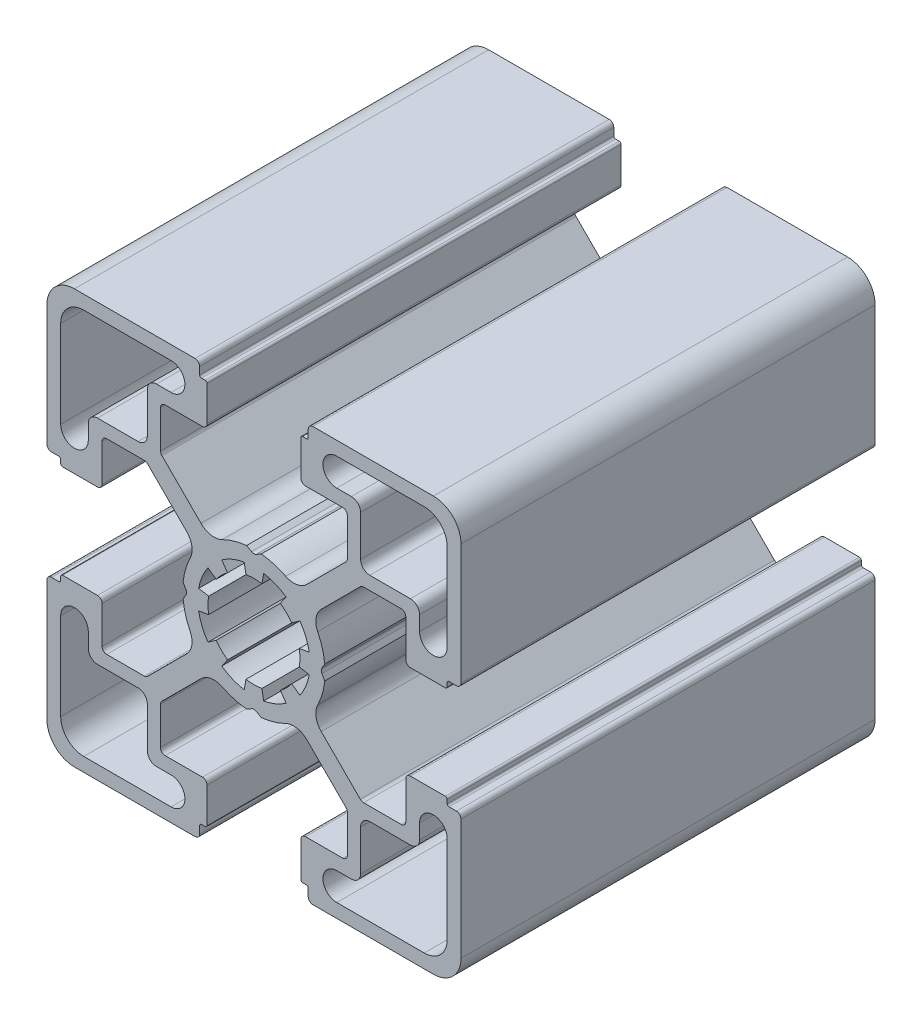
SolidWorks part; units mm, degrees
material "АД31Т ГОСТ 4784-97"
ref_plane "Спереди" through (0, 0, 0) normal (0, 0, 1) x (1, 0, 0)
ref_plane "Сверху" through (0, 0, 0) normal (0, 1, 0) x (1, 0, 0)
ref_plane "Справа" through (0, 0, 0) normal (1, 0, 0) x (0, 0, -1)
sketch "Эскиз1" plane through (0, 0, 0) normal (0, 0, 1) x (1, 0, 0)
  line L1 (11.59, -14.6758) -> (11.59, -12.59)
  line L2 (18.5, 21) -> (9, 21)
  line L3 (-11.59, 14.6758) -> (-11.59, 12.59)
  line L4 (18, 10.59) -> (18, 9)
  line L5 (14.6758, 11.59) -> (17, 11.59)
  line L6 (14.6758, 11.59) -> (12.59, 11.59)
  line L7 (21, 18.5) -> (21, 9)
  line L8 (-7.3858, -0.25) -> (-7.7005, -0.7951)
  line L9 (-2.8679, 4.0958) -> (-3.4988, 4.9968)
  line L10 (-16.5, 5.6) -> (-16.5, 9.65)
  line L11 (-16, 10.15) -> (-11.9127, 10.15)
  line L12 (-22, 5.9) -> (-21.2, 5.9)
  line L13 (-20.8, 5.1) -> (-17, 5.1)
  line L14 (-21, 5.7) -> (-21, 5.3)
  line L15 (-22, 5.9) -> (-21.2, 5.9)
  line L16 (11.59, 14.6758) -> (11.59, 17)
  line L17 (-7.8879, 6.3322) -> (-7.308, 5.7523)
  line L18 (-21, 5.7) -> (-21, 5.3)
  line L19 (-7.8879, 6.3322) -> (-11.5592, 10.0036)
  line L20 (-0.25, 7.3858) -> (-0.7951, 7.7005)
  line L21 (-22.5, 6.4) -> (-22.5, 19.5)
  line L22 (10.59, 18) -> (9, 18)
  line L23 (-0.25, 7.3858) -> (-0.7951, 7.7005)
  line L24 (5.6, 16.5) -> (9.65, 16.5)
  line L25 (-6.4, 22.5) -> (-19.5, 22.5)
  line L26 (10.15, 16) -> (10.15, 11.9127)
  line L27 (-6.3322, 7.8879) -> (-10.0036, 11.5592)
  line L28 (-5.7, 21) -> (-5.3, 21)
  line L29 (-7.3858, 0.25) -> (-7.7005, 0.7951)
  line L30 (-6.3322, 7.8879) -> (-5.7523, 7.308)
  line L31 (-5.9, 22) -> (-5.9, 21.2)
  line L32 (-5.7, 21) -> (-5.3, 21)
  line L33 (-5.1, 20.8) -> (-5.1, 17)
  line L34 (-5.9, 22) -> (-5.9, 21.2)
  line L35 (-10.15, 16) -> (-10.15, 11.9127)
  line L36 (-5.6, 16.5) -> (-9.65, 16.5)
  line L37 (0.25, 7.3858) -> (0.7951, 7.7005)
  line L38 (-10.59, 18) -> (-9, 18)
  line L39 (-11.59, 14.6758) -> (-11.59, 17)
  line L40 (-21, 18.5) -> (-21, 9)
  line L41 (5.9, 22) -> (5.9, 21.2)
  line L42 (-14.6758, 11.59) -> (-12.59, 11.59)
  line L43 (-14.6758, 11.59) -> (-17, 11.59)
  line L44 (-18, 10.59) -> (-18, 9)
  line L45 (5.1, 20.8) -> (5.1, 17)
  line L46 (-18.5, 21) -> (-9, 21)
  line L47 (5.7, 21) -> (5.3, 21)
  line L48 (5.9, 22) -> (5.9, 21.2)
  line L49 (6.3322, 7.8879) -> (5.7523, 7.308)
  line L50 (7.3858, 0.25) -> (7.7005, 0.7951)
  line L51 (5.7, 21) -> (5.3, 21)
  line L52 (6.3322, 7.8879) -> (10.0036, 11.5592)
  line L53 (6.4, 22.5) -> (19.5, 22.5)
  line L54 (22.5, 6.4) -> (22.5, 19.5)
  line L55 (0.25, 7.3858) -> (0.7951, 7.7005)
  line L56 (7.8879, 6.3322) -> (11.5592, 10.0036)
  line L57 (21, 5.7) -> (21, 5.3)
  line L58 (7.8879, 6.3322) -> (7.308, 5.7523)
  line L59 (22, 5.9) -> (21.2, 5.9)
  line L60 (21, 5.7) -> (21, 5.3)
  line L61 (20.8, 5.1) -> (17, 5.1)
  line L62 (22, 5.9) -> (21.2, 5.9)
  line L63 (16, 10.15) -> (11.9127, 10.15)
  line L64 (16.5, 5.6) -> (16.5, 9.65)
  line L65 (7.3858, -0.25) -> (7.7005, -0.7951)
  line L66 (11.59, 14.6758) -> (11.59, 12.59)
  line L67 (7.3858, 0.25) -> (7.7005, 0.7951)
  line L68 (16.5, -5.6) -> (16.5, -9.65)
  line L69 (16, -10.15) -> (11.9127, -10.15)
  line L70 (22, -5.9) -> (21.2, -5.9)
  line L71 (20.8, -5.1) -> (17, -5.1)
  line L72 (21, -5.7) -> (21, -5.3)
  line L73 (22, -5.9) -> (21.2, -5.9)
  line L74 (7.8879, -6.3322) -> (7.308, -5.7523)
  line L75 (21, -5.7) -> (21, -5.3)
  line L76 (7.8879, -6.3322) -> (11.5592, -10.0036)
  line L77 (0.25, -7.3858) -> (0.7951, -7.7005)
  line L78 (22.5, -6.4) -> (22.5, -19.5)
  line L79 (6.4, -22.5) -> (19.5, -22.5)
  line L80 (6.3322, -7.8879) -> (10.0036, -11.5592)
  line L81 (5.7, -21) -> (5.3, -21)
  line L82 (7.3858, -0.25) -> (7.7005, -0.7951)
  line L83 (6.3322, -7.8879) -> (5.7523, -7.308)
  line L84 (5.9, -22) -> (5.9, -21.2)
  line L85 (5.7, -21) -> (5.3, -21)
  line L86 (-18.5, -21) -> (-9, -21)
  line L87 (5.1, -20.8) -> (5.1, -17)
  line L88 (-18, -10.59) -> (-18, -9)
  line L89 (-14.6758, -11.59) -> (-17, -11.59)
  line L90 (-14.6758, -11.59) -> (-12.59, -11.59)
  line L91 (5.9, -22) -> (5.9, -21.2)
  line L92 (-21, -18.5) -> (-21, -9)
  line L93 (-11.59, -14.6758) -> (-11.59, -17)
  line L94 (-10.59, -18) -> (-9, -18)
  line L95 (0.25, -7.3858) -> (0.7951, -7.7005)
  line L96 (-5.6, -16.5) -> (-9.65, -16.5)
  line L97 (-10.15, -16) -> (-10.15, -11.9127)
  line L98 (-5.9, -22) -> (-5.9, -21.2)
  line L99 (-5.1, -20.8) -> (-5.1, -17)
  line L100 (-5.7, -21) -> (-5.3, -21)
  line L101 (-5.9, -22) -> (-5.9, -21.2)
  line L102 (-6.3322, -7.8879) -> (-5.7523, -7.308)
  line L103 (-7.3858, -0.25) -> (-7.7005, -0.7951)
  line L104 (-5.7, -21) -> (-5.3, -21)
  line L105 (-6.3322, -7.8879) -> (-10.0036, -11.5592)
  line L106 (10.15, -16) -> (10.15, -11.9127)
  line L107 (-6.4, -22.5) -> (-19.5, -22.5)
  line L108 (5.6, -16.5) -> (9.65, -16.5)
  line L109 (-0.25, -7.3858) -> (-0.7951, -7.7005)
  line L110 (10.59, -18) -> (9, -18)
  line L111 (-22.5, -6.4) -> (-22.5, -19.5)
  line L112 (-0.25, -7.3858) -> (-0.7951, -7.7005)
  line L113 (-7.8879, -6.3322) -> (-11.5592, -10.0036)
  line L114 (-21, -5.7) -> (-21, -5.3)
  line L115 (-7.8879, -6.3322) -> (-7.308, -5.7523)
  line L116 (11.59, -14.6758) -> (11.59, -17)
  line L117 (-22, -5.9) -> (-21.2, -5.9)
  line L118 (-21, -5.7) -> (-21, -5.3)
  line L119 (-20.8, -5.1) -> (-17, -5.1)
  line L120 (-22, -5.9) -> (-21.2, -5.9)
  line L121 (-16, -10.15) -> (-11.9127, -10.15)
  line L122 (-16.5, -5.6) -> (-16.5, -9.65)
  line L123 (-7.3858, 0.25) -> (-7.7005, 0.7951)
  line L124 (21, -18.5) -> (21, -9)
  line L125 (14.6758, -11.59) -> (12.59, -11.59)
  line L126 (14.6758, -11.59) -> (17, -11.59)
  line L127 (18, -10.59) -> (18, -9)
  line L128 (-11.59, -14.6758) -> (-11.59, -12.59)
  line L129 (18.5, -21) -> (9, -21)
  line L130 (-4.0958, 2.8679) -> (-4.9968, 3.4988)
  line L131 (-0.8682, 4.924) -> (-1.0593, 6.0073)
  line L132 (0.8682, 4.924) -> (1.0593, 6.0073)
  line L134 (-4.924, -0.8682) -> (-6.0073, -1.0593)
  line L135 (-4.924, 0.8682) -> (-6.0073, 1.0593)
  line L136 (0.8682, -4.924) -> (1.0593, -6.0073)
  line L137 (-0.8682, -4.924) -> (-1.0593, -6.0073)
  line L138 (-2.8679, -4.0958) -> (-3.4988, -4.9968)
  line L139 (-4.0958, -2.8679) -> (-4.9968, -3.4988)
  line L140 (-4.924, -0.8682) -> (-6.0073, -1.0593)
  line L141 (-4.924, 0.8682) -> (-6.0073, 1.0593)
  line L142 (2.8679, 4.0958) -> (3.4988, 4.9968)
  line L143 (4.0958, 2.8679) -> (4.9968, 3.4988)
  line L144 (4.924, 0.8682) -> (6.0073, 1.0593)
  line L145 (4.924, -0.8682) -> (6.0073, -1.0593)
  line L146 (4.0958, -2.8679) -> (4.9968, -3.4988)
  line L147 (2.8679, -4.0958) -> (3.4988, -4.9968)
  arc A0 (-2.8679, 4.0958) -> (-4.0958, 2.8679) centre (0, 0) ccw
  arc A1 (-4.9968, 3.4988) -> (-6.0073, 1.0593) centre (0, 0) ccw
  arc A2 (-19.5, 22.5) -> (-22.5, 19.5) centre (-19.5, 19.5) ccw
  arc A3 (-11.5592, 10.0036) -> (-11.9127, 10.15) centre (-11.9127, 9.65) ccw
  arc A4 (-16, 10.15) -> (-16.5, 9.65) centre (-16, 9.65) ccw
  arc A5 (-17, 5.1) -> (-16.5, 5.6) centre (-17, 5.6) ccw
  arc A6 (-22.5, 6.4) -> (-22, 5.9) centre (-22, 6.4) ccw
  arc A7 (-20.8, 5.1) -> (-21, 5.3) centre (-20.8, 5.3) cw
  arc A8 (-21.2, 5.9) -> (-21, 5.7) centre (-21.2, 5.7) cw
  arc A9 (-6.9314, 3.4475) -> (-7.7005, 0.7951) centre (0, 0) ccw
  arc A10 (10.59, 18) -> (11.59, 17) centre (10.59, 17) cw
  arc A11 (9, 21) -> (9, 18) centre (9, 19.5) ccw
  arc A12 (17, 11.59) -> (18, 10.59) centre (17, 10.59) cw
  arc A13 (12.59, 11.59) -> (11.59, 12.59) centre (12.59, 12.59) cw
  arc A14 (21, 9) -> (18, 9) centre (19.5, 9) cw
  arc A15 (21, 18.5) -> (18.5, 21) centre (18.5, 18.5) ccw
  arc A16 (-7.308, 5.7523) -> (-6.9314, 3.4475) centre (-8.7222, 4.3381) cw
  arc A17 (-5.9, 21.2) -> (-5.7, 21) centre (-5.7, 21.2) ccw
  arc A18 (-7.3858, -0.25) -> (-7.3858, 0.25) centre (-7.8188, 0) ccw
  arc A19 (-22.5, 6.4) -> (-22, 5.9) centre (-22, 6.4) ccw
  arc A20 (-21.2, 5.9) -> (-21, 5.7) centre (-21.2, 5.7) cw
  arc A21 (-6.4, 22.5) -> (-5.9, 22) centre (-6.4, 22) cw
  arc A22 (0.25, 7.3858) -> (-0.25, 7.3858) centre (0, 7.8188) cw
  arc A23 (-5.7523, 7.308) -> (-3.4475, 6.9314) centre (-4.3381, 8.7222) ccw
  arc A24 (-3.4475, 6.9314) -> (-0.7951, 7.7005) centre (0, 0) cw
  arc A25 (-5.9, 21.2) -> (-5.7, 21) centre (-5.7, 21.2) ccw
  arc A26 (-5.1, 20.8) -> (-5.3, 21) centre (-5.3, 20.8) ccw
  arc A27 (-6.4, 22.5) -> (-5.9, 22) centre (-6.4, 22) cw
  arc A28 (-5.1, 17) -> (-5.6, 16.5) centre (-5.6, 17) cw
  arc A29 (-10.15, 16) -> (-9.65, 16.5) centre (-9.65, 16) cw
  arc A30 (-10.0036, 11.5592) -> (-10.15, 11.9127) centre (-9.65, 11.9127) cw
  arc A31 (-21, 18.5) -> (-18.5, 21) centre (-18.5, 18.5) cw
  arc A32 (-21, 9) -> (-18, 9) centre (-19.5, 9) ccw
  arc A33 (-12.59, 11.59) -> (-11.59, 12.59) centre (-12.59, 12.59) ccw
  arc A34 (-17, 11.59) -> (-18, 10.59) centre (-17, 10.59) ccw
  arc A35 (-9, 21) -> (-9, 18) centre (-9, 19.5) cw
  arc A36 (-10.59, 18) -> (-11.59, 17) centre (-10.59, 17) ccw
  arc A37 (10.0036, 11.5592) -> (10.15, 11.9127) centre (9.65, 11.9127) ccw
  arc A38 (10.15, 16) -> (9.65, 16.5) centre (9.65, 16) ccw
  arc A39 (5.1, 17) -> (5.6, 16.5) centre (5.6, 17) ccw
  arc A40 (6.4, 22.5) -> (5.9, 22) centre (6.4, 22) ccw
  arc A41 (5.1, 20.8) -> (5.3, 21) centre (5.3, 20.8) cw
  arc A42 (5.9, 21.2) -> (5.7, 21) centre (5.7, 21.2) cw
  arc A43 (3.4475, 6.9314) -> (0.7951, 7.7005) centre (0, 0) ccw
  arc A44 (5.7523, 7.308) -> (3.4475, 6.9314) centre (4.3381, 8.7222) cw
  arc A45 (6.4, 22.5) -> (5.9, 22) centre (6.4, 22) ccw
  arc A46 (21.2, 5.9) -> (21, 5.7) centre (21.2, 5.7) ccw
  arc A47 (22.5, 6.4) -> (22, 5.9) centre (22, 6.4) cw
  arc A48 (7.3858, -0.25) -> (7.3858, 0.25) centre (7.8188, 0) cw
  arc A49 (5.9, 21.2) -> (5.7, 21) centre (5.7, 21.2) cw
  arc A50 (7.308, 5.7523) -> (6.9314, 3.4475) centre (8.7222, 4.3381) ccw
  arc A51 (6.9314, 3.4475) -> (7.7005, 0.7951) centre (0, 0) cw
  arc A52 (21.2, 5.9) -> (21, 5.7) centre (21.2, 5.7) ccw
  arc A53 (20.8, 5.1) -> (21, 5.3) centre (20.8, 5.3) ccw
  arc A54 (22.5, 6.4) -> (22, 5.9) centre (22, 6.4) cw
  arc A55 (17, 5.1) -> (16.5, 5.6) centre (17, 5.6) cw
  arc A56 (16, 10.15) -> (16.5, 9.65) centre (16, 9.65) cw
  arc A57 (11.5592, 10.0036) -> (11.9127, 10.15) centre (11.9127, 9.65) cw
  arc A58 (19.5, 22.5) -> (22.5, 19.5) centre (19.5, 19.5) cw
  arc A59 (19.5, -22.5) -> (22.5, -19.5) centre (19.5, -19.5) ccw
  arc A60 (11.5592, -10.0036) -> (11.9127, -10.15) centre (11.9127, -9.65) ccw
  arc A61 (16, -10.15) -> (16.5, -9.65) centre (16, -9.65) ccw
  arc A62 (17, -5.1) -> (16.5, -5.6) centre (17, -5.6) ccw
  arc A63 (22.5, -6.4) -> (22, -5.9) centre (22, -6.4) ccw
  arc A64 (20.8, -5.1) -> (21, -5.3) centre (20.8, -5.3) cw
  arc A65 (21.2, -5.9) -> (21, -5.7) centre (21.2, -5.7) cw
  arc A66 (6.9314, -3.4475) -> (7.7005, -0.7951) centre (0, 0) ccw
  arc A67 (7.308, -5.7523) -> (6.9314, -3.4475) centre (8.7222, -4.3381) cw
  arc A68 (5.9, -21.2) -> (5.7, -21) centre (5.7, -21.2) ccw
  arc A69 (22.5, -6.4) -> (22, -5.9) centre (22, -6.4) ccw
  arc A70 (21.2, -5.9) -> (21, -5.7) centre (21.2, -5.7) cw
  arc A71 (6.4, -22.5) -> (5.9, -22) centre (6.4, -22) cw
  arc A72 (5.7523, -7.308) -> (3.4475, -6.9314) centre (4.3381, -8.7222) ccw
  arc A73 (3.4475, -6.9314) -> (0.7951, -7.7005) centre (0, 0) cw
  arc A74 (5.9, -21.2) -> (5.7, -21) centre (5.7, -21.2) ccw
  arc A75 (5.1, -20.8) -> (5.3, -21) centre (5.3, -20.8) ccw
  arc A76 (6.4, -22.5) -> (5.9, -22) centre (6.4, -22) cw
  arc A77 (5.1, -17) -> (5.6, -16.5) centre (5.6, -17) cw
  arc A78 (10.15, -16) -> (9.65, -16.5) centre (9.65, -16) cw
  arc A79 (10.0036, -11.5592) -> (10.15, -11.9127) centre (9.65, -11.9127) cw
  arc A80 (-10.59, -18) -> (-11.59, -17) centre (-10.59, -17) cw
  arc A81 (-9, -21) -> (-9, -18) centre (-9, -19.5) ccw
  arc A82 (-17, -11.59) -> (-18, -10.59) centre (-17, -10.59) cw
  arc A83 (-12.59, -11.59) -> (-11.59, -12.59) centre (-12.59, -12.59) cw
  arc A84 (-21, -9) -> (-18, -9) centre (-19.5, -9) cw
  arc A85 (-21, -18.5) -> (-18.5, -21) centre (-18.5, -18.5) ccw
  arc A86 (-10.0036, -11.5592) -> (-10.15, -11.9127) centre (-9.65, -11.9127) ccw
  arc A87 (-10.15, -16) -> (-9.65, -16.5) centre (-9.65, -16) ccw
  arc A88 (-5.1, -17) -> (-5.6, -16.5) centre (-5.6, -17) ccw
  arc A89 (-6.4, -22.5) -> (-5.9, -22) centre (-6.4, -22) ccw
  arc A90 (-5.1, -20.8) -> (-5.3, -21) centre (-5.3, -20.8) cw
  arc A91 (-5.9, -21.2) -> (-5.7, -21) centre (-5.7, -21.2) cw
  arc A92 (-3.4475, -6.9314) -> (-0.7951, -7.7005) centre (0, 0) ccw
  arc A93 (-5.7523, -7.308) -> (-3.4475, -6.9314) centre (-4.3381, -8.7222) cw
  arc A94 (0.25, -7.3858) -> (-0.25, -7.3858) centre (0, -7.8188) ccw
  arc A95 (-6.4, -22.5) -> (-5.9, -22) centre (-6.4, -22) ccw
  arc A96 (-21.2, -5.9) -> (-21, -5.7) centre (-21.2, -5.7) ccw
  arc A97 (-22.5, -6.4) -> (-22, -5.9) centre (-22, -6.4) cw
  arc A98 (-5.9, -21.2) -> (-5.7, -21) centre (-5.7, -21.2) cw
  arc A99 (-7.308, -5.7523) -> (-6.9314, -3.4475) centre (-8.7222, -4.3381) ccw
  arc A100 (21, -18.5) -> (18.5, -21) centre (18.5, -18.5) cw
  arc A101 (21, -9) -> (18, -9) centre (19.5, -9) ccw
  arc A102 (12.59, -11.59) -> (11.59, -12.59) centre (12.59, -12.59) ccw
  arc A103 (17, -11.59) -> (18, -10.59) centre (17, -10.59) ccw
  arc A104 (9, -21) -> (9, -18) centre (9, -19.5) cw
  arc A105 (10.59, -18) -> (11.59, -17) centre (10.59, -17) ccw
  arc A106 (-6.9314, -3.4475) -> (-7.7005, -0.7951) centre (0, 0) cw
  arc A107 (-21.2, -5.9) -> (-21, -5.7) centre (-21.2, -5.7) ccw
  arc A108 (-20.8, -5.1) -> (-21, -5.3) centre (-20.8, -5.3) ccw
  arc A109 (-22.5, -6.4) -> (-22, -5.9) centre (-22, -6.4) cw
  arc A110 (-17, -5.1) -> (-16.5, -5.6) centre (-17, -5.6) cw
  arc A111 (-16, -10.15) -> (-16.5, -9.65) centre (-16, -9.65) cw
  arc A112 (-11.5592, -10.0036) -> (-11.9127, -10.15) centre (-11.9127, -9.65) cw
  arc A113 (-19.5, -22.5) -> (-22.5, -19.5) centre (-19.5, -19.5) cw
  arc A114 (-1.0593, 6.0073) -> (-3.4988, 4.9968) centre (0, 0) ccw
  arc A115 (0.8682, 4.924) -> (-0.8682, 4.924) centre (0, 0) ccw
  arc A116 (3.4988, 4.9968) -> (1.0593, 6.0073) centre (0, 0) ccw
  arc A117 (4.0958, 2.8679) -> (2.8679, 4.0958) centre (0, 0) ccw
  arc A118 (4.924, -0.8682) -> (4.924, 0.8682) centre (0, 0) ccw
  arc A119 (6.0073, 1.0593) -> (4.9968, 3.4988) centre (0, 0) ccw
  arc A120 (2.8679, -4.0958) -> (4.0958, -2.8679) centre (0, 0) ccw
  arc A121 (4.9968, -3.4988) -> (6.0073, -1.0593) centre (0, 0) ccw
  arc A122 (-0.8682, -4.924) -> (0.8682, -4.924) centre (0, 0) ccw
  arc A123 (1.0593, -6.0073) -> (3.4988, -4.9968) centre (0, 0) ccw
  arc A124 (-4.0958, -2.8679) -> (-2.8679, -4.0958) centre (0, 0) ccw
  arc A125 (-3.4988, -4.9968) -> (-1.0593, -6.0073) centre (0, 0) ccw
  arc A126 (-4.924, 0.8682) -> (-4.924, -0.8682) centre (0, 0) ccw
  arc A127 (-6.0073, -1.0593) -> (-4.9968, -3.4988) centre (0, 0) ccw
  point P66 (-7.7414, -0.866)
  point P69 (-7.7414, 0.866)
  point P73 (-22.5, 5.9)
  point P96 (-5.9, 22.5)
  point P97 (-0.866, 7.7414)
  point P98 (0.866, 7.7414)
  point P168 (5.9, 22.5)
  point P169 (22.5, 5.9)
  point P170 (7.7414, 0.866)
  point P171 (7.7414, -0.866)
  point P310 (22.5, -5.9)
  point P311 (5.9, -22.5)
  point P312 (0.866, -7.7414)
  point P313 (-0.866, -7.7414)
  point P314 (-5.9, -22.5)
  point P315 (-22.5, -5.9)
extrude "Бобышка-Вытянуть1" add sketch "Эскиз1" along normal blind 45 contours A113 L107 A89 L98 A91 L100 A90 L99 A88 L96 A87 L97 A86 L105 L102 A93 A92 L109 A94 L77 A73 A72 L83 L80 A79 L106 A78 L108 A77 L87 A75 L81 A68 L84 A71 L79 A59 L78 A63 L70 A65 L72 A64 L71 A62 L68 A61 L69 A60 L76 L74
